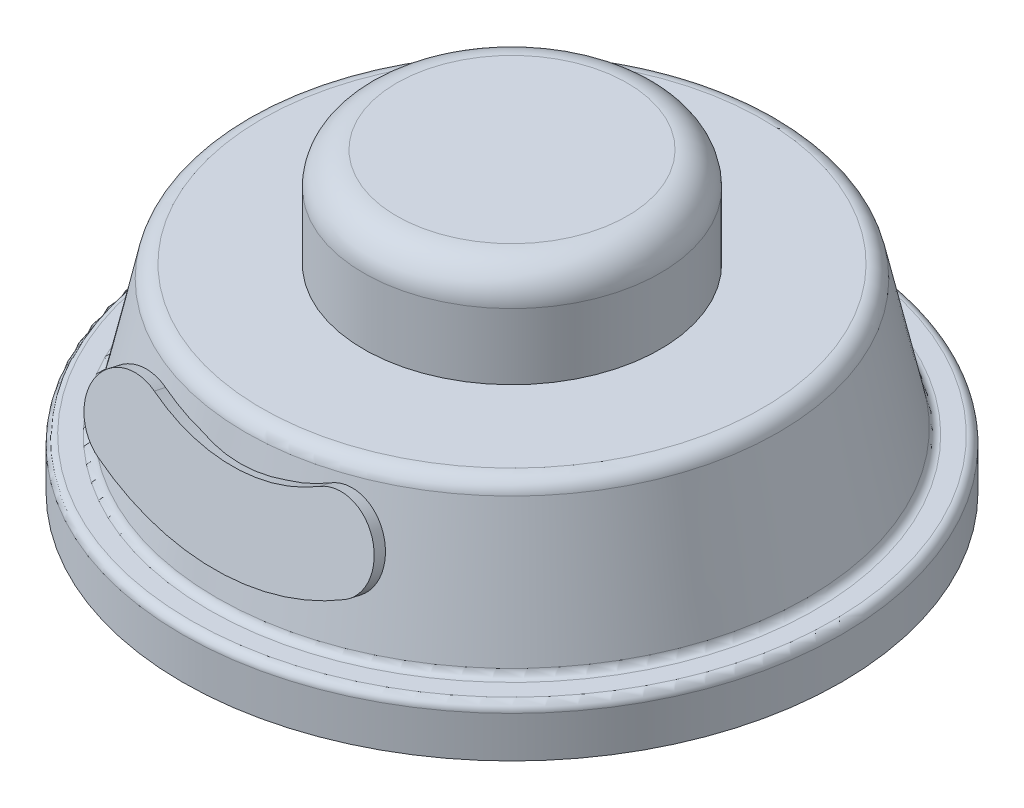
SolidWorks part; units mm, degrees
ref_plane "前视基准面" through (0, 0, 0) normal (0, 0, 1) x (1, 0, 0)
ref_plane "上视基准面" through (0, 0, 0) normal (0, 1, 0) x (1, 0, 0)
ref_plane "右视基准面" through (0, 0, 0) normal (1, 0, 0) x (0, 0, -1)
other "Configuration Table"
sketch "草图1" plane through (0, 0, 0) normal (0, 1, 0) x (1, 0, 0)
  circle A0 centre (0, 0) radius 20
  dimension "D1" = 40
extrude "凸台-拉伸1" add sketch "草图1" along normal blind 3
sketch "草图3" plane through (0, 0, 0) normal (0, 0, 1) x (1, 0, 0)
  line L0 (0, 3) -> (-18, 3)
  line L1 (20, 3) -> (-20, 3) construction
  line L2 (-18, 3) -> (-16, 12)
  line L3 (-16, 12) -> (0, 12)
  line L4 (0, 12) -> (0, 3)
  dimension "D1" = 18
  dimension "D2" = 16
  dimension "D3" = 9
revolve "旋转1" add sketch "草图3" angle 360 about L4
sketch "草图4" plane through (0, 12, 0) normal (0, 1, 0) x (1, 0, 0)
  circle A0 centre (0, 0) radius 9
  dimension "D1" = 18
extrude "凸台-拉伸2" add sketch "草图4" along normal blind 6
fillet "圆角1" radius 2 1 edges at (-9, 18, 0)
fillet "圆角2" radius 1 1 edges at (-16, 12, 0)
sketch "草图5" plane through (0, 0, 0) normal (0, 0, 1) x (1, 0, 0)
  line L0 (-20, 0) -> (20, 0) construction
  line L1 (-13.3708, 0.6038) -> (-10, 3.5)
  line L2 (-17.5, 0) -> (-17.5, 2.5)
  line L3 (-6.8221, 2) -> (7.9413, 2) construction
  line L5 (0, 2) -> (0, 0)
  line L6 (-17.5, 0) -> (0, 0)
  line L7 (-20, 3) -> (-20, 0) construction
  line L8 (-20, 0) -> (-20, 1)
  line L9 (-20, 1) -> (-19.5, 1)
  line L10 (-19.5, 1) -> (-19.5, 0)
  line L11 (-19.5, 0) -> (-17.5, 0)
  line L12 (-19.5, 0) -> (-20, 0)
  arc A0 (-17.5, 2.5) -> (-13.3708, 0.6038) centre (-15, 2.5) ccw
  arc A1 (-10, 3.5) -> (0, 2) centre (0, 36.0833) ccw
  dimension "D4" = 2.5
  dimension "D1" = 2
  dimension "D2" = 2.5
  dimension "D3" = 3.5
  dimension "D5" = 10
  dimension "D6" = 0.5
  dimension "D7" = 1
revolve "切除-旋转1" cut sketch "草图5" angle 360 about L5
fillet "圆角3" radius 0.5 2 edges at (0, 3, 20) (-18, 3, 0)
ref_plane "基准面1" through (0, 3.9529, 17.7882) normal (0, 0.2169, 0.9762) x (1, 0, 0)
sketch "草图6" plane through (0, 3.9529, 17.7882) normal (0, 0.2169, 0.9762) x (1, 0, 0)
  line L0 (0, 7.4412) -> (0, -0.5751) construction
  line L1 (-13.0187, 3.433) -> (8.9906, 3.433) construction
  line L3 (-1, 4.433) -> (1, 4.433)
  line L4 (-1, 4.433) -> (-1, 2.433)
  line L5 (-1, 2.433) -> (1, 2.433)
  line L6 (1, 4.433) -> (1, 2.433)
  line L7 (-1, 4.433) -> (1, 2.433) construction
  line L8 (-1, 2.433) -> (1, 4.433) construction
  arc A0 (-6.25, 5.0894) -> (6.25, 5.0894) centre (0, 16.0529) ccw construction
  arc A1 (-7.4881, 2.9175) -> (7.4881, 2.9175) centre (0, 16.0529) ccw
  arc A2 (-5.0119, 7.2613) -> (5.0119, 7.2613) centre (0, 16.0529) ccw
  arc A3 (-5.0119, 7.2613) -> (-7.4881, 2.9175) centre (-6.25, 5.0894) ccw
  arc A4 (7.4881, 2.9175) -> (5.0119, 7.2613) centre (6.25, 5.0894) ccw
  ellipse E0 centre (0, 10.9498) end of major axis (-16.174, 10.9498) minor radius 3.5086 construction
  ellipse E1 centre (0, 3.3108) end of major axis (17.913, 3.3108) minor radius 3.8859 construction
  ellipse E2 centre (0, 17.5714) end of major axis (7, 17.5714) minor radius 1.5185 construction
  point P18 (0, 3.433)
  point P24 (0, 3.433)
  point P27 (0, 3.433)
  dimension "D2" = 5
  dimension "D1" = 12.5
  dimension "D3" = 2
  dimension "D4" = 2
extrude "凸台-拉伸3" add sketch "草图6" along normal blind 0.7 from offset 0.2 contours A1 A4 A2 A3 L3 L6 L5 L4 | L6 L3 L4 L5 offset against normal yes
